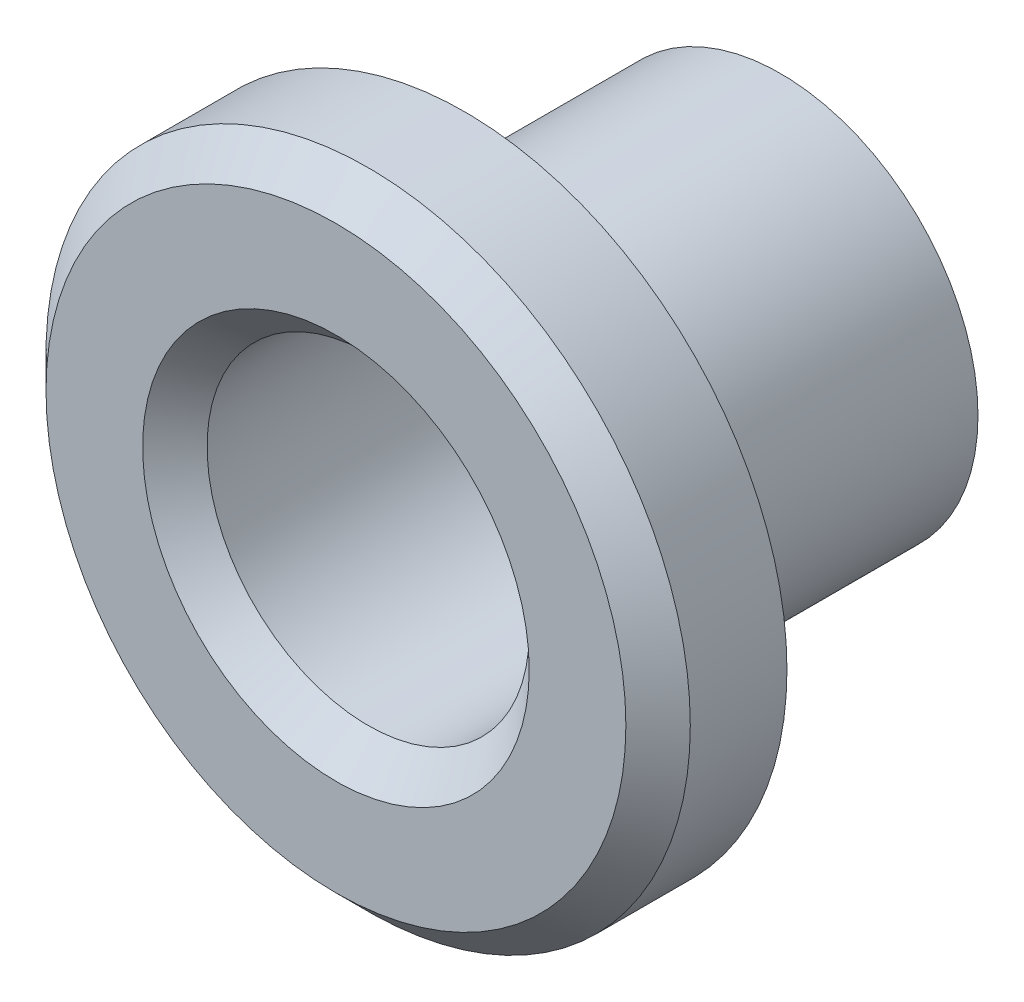
SolidWorks part; units mm, degrees
ref_plane "Front Plane" through (0, 0, 0) normal (0, 0, 1) x (1, 0, 0)
ref_plane "Top Plane" through (0, 0, 0) normal (0, 1, 0) x (1, 0, 0)
ref_plane "Right Plane" through (0, 0, 0) normal (1, 0, 0) x (0, 0, -1)
sketch "Sketch1" plane through (0, 0, 0) normal (0, 0, 1) x (1, 0, 0)
  circle A0 centre (0, 0) radius 3.065
  dimension "D1" = 6.13
extrude "Boss-Extrude1" add sketch "Sketch1" along normal blind 4.9
sketch "Sketch2" plane through (0, 0, 4.9) normal (0, 0, 1) x (1, 0, 0)
  circle A0 centre (0, 0) radius 5
extrude "Boss-Extrude2" add sketch "Sketch2" along normal blind 2
sketch "Sketch3" plane through (0, 0, 6.9) normal (0, 0, 1) x (1, 0, 0)
  circle A0 centre (0, 0) radius 2.5
extrude "Cut-Extrude1" cut sketch "Sketch3" against normal through all
chamfer "Chamfer1" distance 0.5 angle 45 1 edges at (5, 0, 6.9)
chamfer "Chamfer2" distance 0.5 angle 45 1 edges at (2.5, 0, 6.9)
